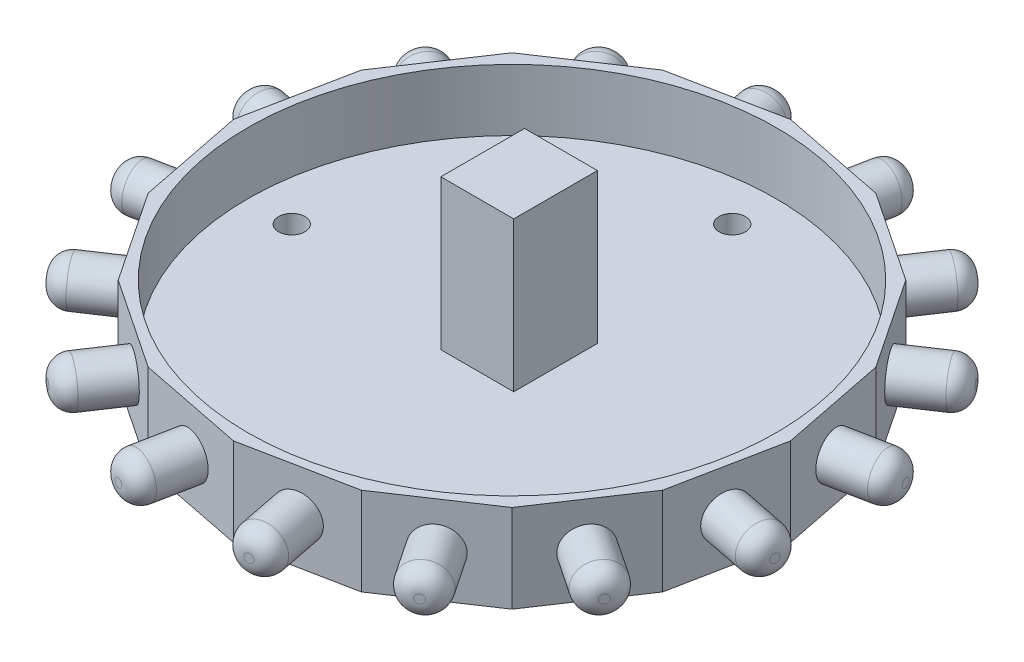
SolidWorks part; units mm, degrees
ref_plane "Face" through (0, 0, 0) normal (0, 0, 1) x (1, 0, 0)
ref_plane "Dessus" through (0, 0, 0) normal (0, 1, 0) x (1, 0, 0)
ref_plane "Droite" through (0, 0, 0) normal (1, 0, 0) x (0, 0, -1)
sketch "Esquisse1" plane through (0, 0, 0) normal (0, 1, 0) x (1, 0, 0)
  line L0 (0, 31.6073) -> (0, -31.6073) construction
  line L1 (0, 31.6073) -> (-12.0956, 29.2014)
  line L2 (-12.0956, 29.2014) -> (-22.3498, 22.3498)
  line L3 (-22.3498, 22.3498) -> (-29.2014, 12.0956)
  line L4 (-29.2014, 12.0956) -> (-31.6073, 0)
  line L5 (-31.6073, 0) -> (-29.2014, -12.0956)
  line L6 (-29.2014, -12.0956) -> (-22.3498, -22.3498)
  line L7 (-22.3498, -22.3498) -> (-12.0956, -29.2014)
  line L8 (-12.0956, -29.2014) -> (0, -31.6073)
  line L9 (0, -31.6073) -> (12.0956, -29.2014)
  line L10 (12.0956, -29.2014) -> (22.3498, -22.3498)
  line L11 (22.3498, -22.3498) -> (29.2014, -12.0956)
  line L12 (29.2014, -12.0956) -> (31.6073, 0)
  line L13 (31.6073, 0) -> (29.2014, 12.0956)
  line L14 (29.2014, 12.0956) -> (22.3498, 22.3498)
  line L15 (22.3498, 22.3498) -> (12.0956, 29.2014)
  line L16 (12.0956, 29.2014) -> (0, 31.6073)
  line L17 (-31.6073, 0) -> (31.6073, 0) construction
  circle A0 centre (0, 0) radius 31 construction
  circle A1 centre (0, 25) radius 1.5
  circle A2 centre (-25, 0) radius 1.5
  circle A3 centre (0, -25) radius 1.5
  circle A4 centre (25, 0) radius 1.5
  dimension "D1" = 3
  dimension "D2" = 62
  dimension "D3" = 25
  dimension "D4" = 25
extrude "Extrusion1" add sketch "Esquisse1" along normal blind 10
sketch "Esquisse3" plane through (0, 10, 0) normal (0, 1, 0) x (1, 0, 0)
  circle A0 centre (0, 0) radius 30
  dimension "D1" = 60
extrude "Extrusion3" cut sketch "Esquisse3" against normal blind 7
sketch "Esquisse4" plane through (6.0478, 0, 30.4043) normal (0.1951, 0, 0.9808) x (0.9808, 0, -0.1951)
  line L0 (0, 10) -> (0, 0) construction
  line L1 (-6.1663, 10) -> (6.1663, 10) construction
  line L2 (-6.1663, 0) -> (6.1663, 0) construction
  line L3 (-6.1663, 5) -> (6.1663, 5) construction
  line L4 (-6.1663, 10) -> (-6.1663, 0) construction
  line L5 (6.1663, 10) -> (6.1663, 0) construction
  circle A0 centre (0, 5) radius 2.5
  dimension "D1" = 5
extrude "Extrusion4" add sketch "Esquisse4" along normal blind 7
fillet "Congé1" radius 2 1 edges at (9.8654, 5, 36.7821)
pattern_circular "Répétition circulaire1" count 16 over 360 about axis through (0, 0, 0) along (0, 1, 0) of "Extrusion4", "Congé1"
sketch "Esquisse5" plane through (0, 3, 0) normal (0, 1, 0) x (1, 0, 0)
  line L1 (4.0759, -3.8782) -> (-4.1987, -3.8782)
  line L2 (4.0759, -3.8782) -> (4.0759, 5.6223)
  line L3 (4.0759, 5.6223) -> (-4.1987, 5.6223)
  line L4 (-4.1987, -3.8782) -> (-4.1987, 5.6223)
extrude "Extrusion5" add sketch "Esquisse5" along normal blind 17
